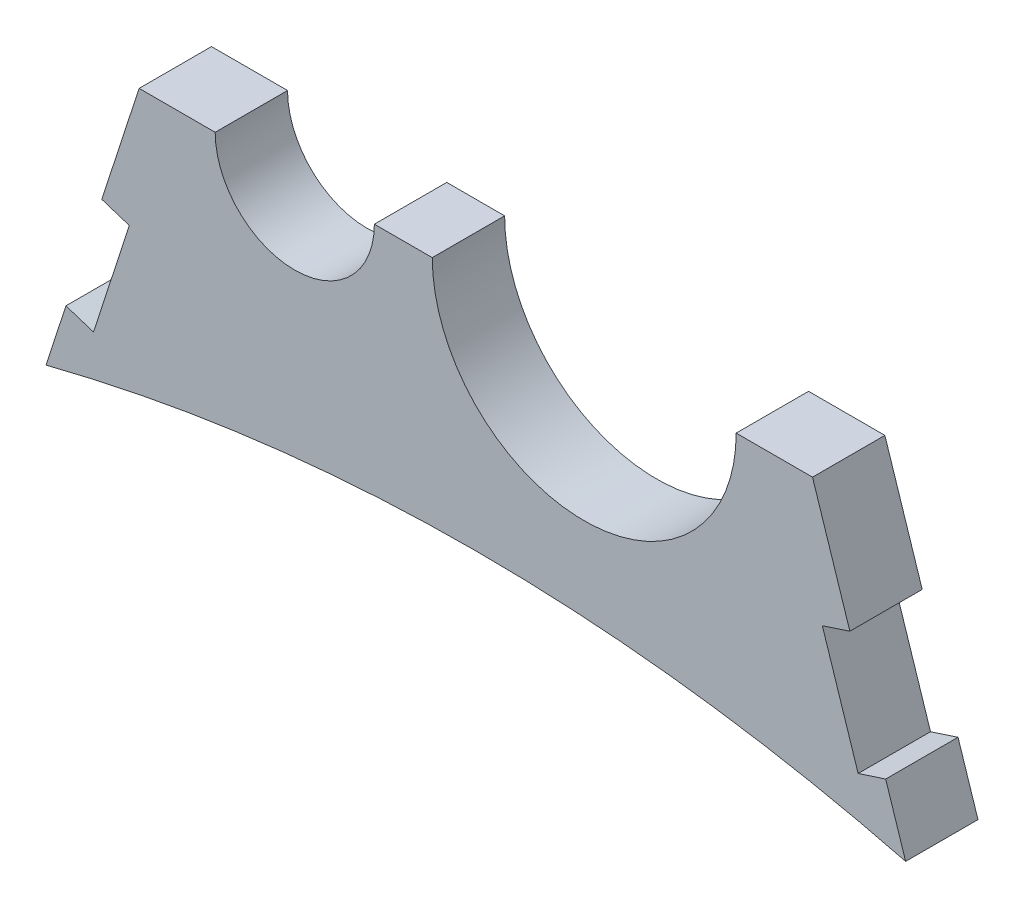
SolidWorks part; units mm, degrees
ref_plane "Front Plane" through (0, 0, 0) normal (0, 0, 1) x (1, 0, 0)
ref_plane "Top Plane" through (0, 0, 0) normal (0, 1, 0) x (1, 0, 0)
ref_plane "Right Plane" through (0, 0, 0) normal (1, 0, 0) x (0, 0, -1)
sketch "Sketch1" plane through (0, 0, 0) normal (0, 0, 1) x (1, 0, 0)
  line L0 (0, 0) -> (0, 324.652) construction
  line L1 (30.7076, 181.3003) -> (24.6961, 151.9943) construction
  line L2 (37.137, 149.4423) -> (40.6988, 166.8059) construction
  line L3 (-37.137, 149.4423) -> (-40.6988, 166.8059) construction
  line L4 (-30.7076, 181.3003) -> (-24.6961, 151.9943) construction
  line L5 (0, 0) -> (-38.8975, 189.6253) construction
  line L6 (27.6276, 178.6698) -> (37.137, 149.4423) construction
  line L7 (0, 0) -> (38.8975, 189.6253) construction
  line L12 (30.2004, 175.8931) -> (45.4337, 129.0731) construction
  line L13 (-27.6276, 178.6698) -> (-37.137, 149.4423) construction
  line L14 (-30.2004, 175.8931) -> (-45.4337, 129.0731) construction
  line L22 (37.7172, 147.659) -> (35.9655, 153.043)
  line L25 (-37.7172, 147.659) -> (-35.9655, 153.043)
  line L34 (-32.822, 162.7045) -> (-30.4067, 161.9187)
  line L35 (-30.4067, 161.9187) -> (-33.5501, 152.2572)
  line L36 (-33.5501, 152.2572) -> (-35.9655, 153.043)
  line L37 (33.5501, 152.2572) -> (35.9655, 153.043)
  line L38 (30.4067, 161.9187) -> (33.5501, 152.2572)
  line L39 (32.822, 162.7045) -> (30.4067, 161.9187)
  line L46 (-29.5452, 172.7758) -> (-22.8727, 172.7758)
  line L47 (-29.5452, 172.7758) -> (-32.822, 162.7045)
  line L48 (29.5452, 172.7758) -> (32.822, 162.7045)
  line L49 (-8.9027, 172.7758) -> (-3.8227, 172.7758)
  line L50 (22.8473, 172.7758) -> (29.5452, 172.7758)
  circle A0 centre (0, 0) radius 152.4 construction
  circle A1 centre (9.5123, 172.7758) radius 12.7 construction
  circle A2 centre (9.5123, 172.7758) radius 19.05 construction
  circle A3 centre (-15.8877, 172.7758) radius 6.35 construction
  circle A4 centre (-15.8877, 172.7758) radius 12.7 construction
  circle A5 centre (0, 0) radius 153.9875 construction
  circle A8 centre (0, 149.4423) radius 44.248 construction
  circle A10 centre (0, 149.4423) radius 45.8355 construction
  arc A33 (37.7172, 147.659) -> (-37.7172, 147.659) centre (0, 0) ccw
  arc A38 (-22.8727, 172.7758) -> (-8.9027, 172.7758) centre (-15.8877, 172.7758) ccw
  arc A39 (-3.8227, 172.7758) -> (22.8473, 172.7758) centre (9.5123, 172.7758) ccw
  dimension "D1" = 304.8
  dimension "D2" = 25.4
  dimension "D3" = 13.97
  dimension "D4" = 38.1
  dimension "D5" = 12.7
  dimension "D6" = 9.5123
  dimension "D8" = 307.975
  dimension "D7" = 33.5501
  dimension "D11" = 88.496
  dimension "D12" = 91.671
  dimension "D13" = 1.5875
  dimension "D14" = 26.67
  dimension "D20" = 25.4
  dimension "D9" = 6.35
  dimension "D10" = 6.35
  dimension "D17" = 2.54
  dimension "D18" = 10.16
extrude "Boss-Extrude2" add sketch "Sketch1" along normal blind 6.35
